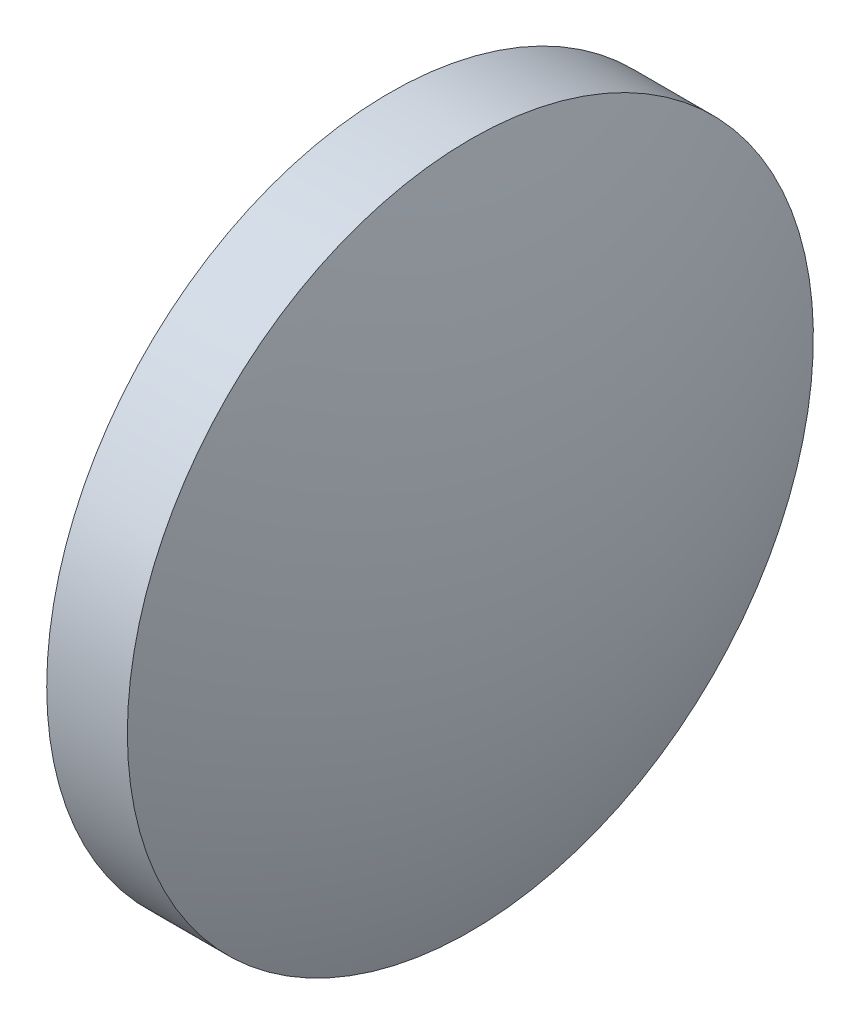
SolidWorks part; units mm, degrees
ref_plane "前视基准面" through (0, 0, 0) normal (0, 0, 1) x (1, 0, 0)
ref_plane "上视基准面" through (0, 0, 0) normal (0, 1, 0) x (1, 0, 0)
ref_plane "右视基准面" through (0, 0, 0) normal (1, 0, 0) x (0, 0, -1)
sketch "草图1" plane through (0, 0, 0) normal (0, 0, 1) x (1, 0, 0)
  line L0 (110.1654, 65.2336) -> (128.9614, 65.2336) construction
  line L1 (115.7736, 65.2336) -> (115.7736, 77.9336)
  line L2 (115.7736, 77.9336) -> (118.7595, 77.9336)
  line L3 (121.1816, 65.2336) -> (115.7736, 65.2336)
  arc A0 (121.1816, 65.2336) -> (118.7595, 77.9336) centre (86.6756, 65.2336) ccw
  dimension "D1" = 34.506
  dimension "D2" = 5.408
revolve "旋转1" add sketch "草图1" angle 360 about L0
